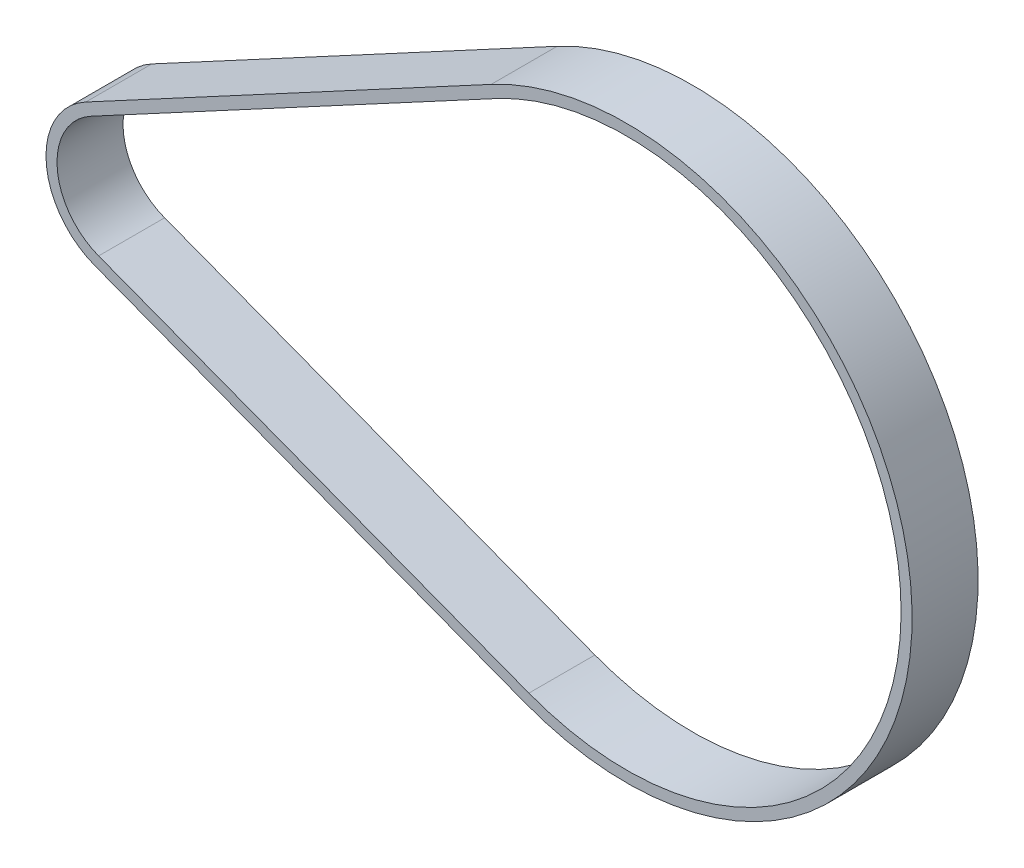
SolidWorks part; units mm, degrees
ref_plane "Front Plane" through (0, 0, 0) normal (0, 0, 1) x (1, 0, 0)
ref_plane "Top Plane" through (0, 0, 0) normal (0, 1, 0) x (1, 0, 0)
ref_plane "Right Plane" through (0, 0, 0) normal (1, 0, 0) x (0, 0, -1)
sketch "Sketch2" plane through (0, 0, 0) normal (0, 0, 1) x (1, 0, 0)
  line L0 (0, 0) -> (1, 0) construction
  line L1 (0, 0) -> (0, 1) construction
  line L4 (36.9486, -24.3097) -> (-2.1662, -9.4493)
  line L5 (-2.9201, 2.1066) -> (33.9323, 21.9232)
  arc A1 (33.9323, 21.9232) -> (36.9486, -24.3097) centre (45.9925, -0.5048) cw
  arc A2 (-2.1662, -9.4493) -> (-2.9201, 2.1066) centre (0.0943, -3.4993) cw
extrude "Extrude-Thin1" add sketch "Sketch2" against normal blind 6 from offset 1.5 thin thin type mid plane wall 1 offset against normal yes
